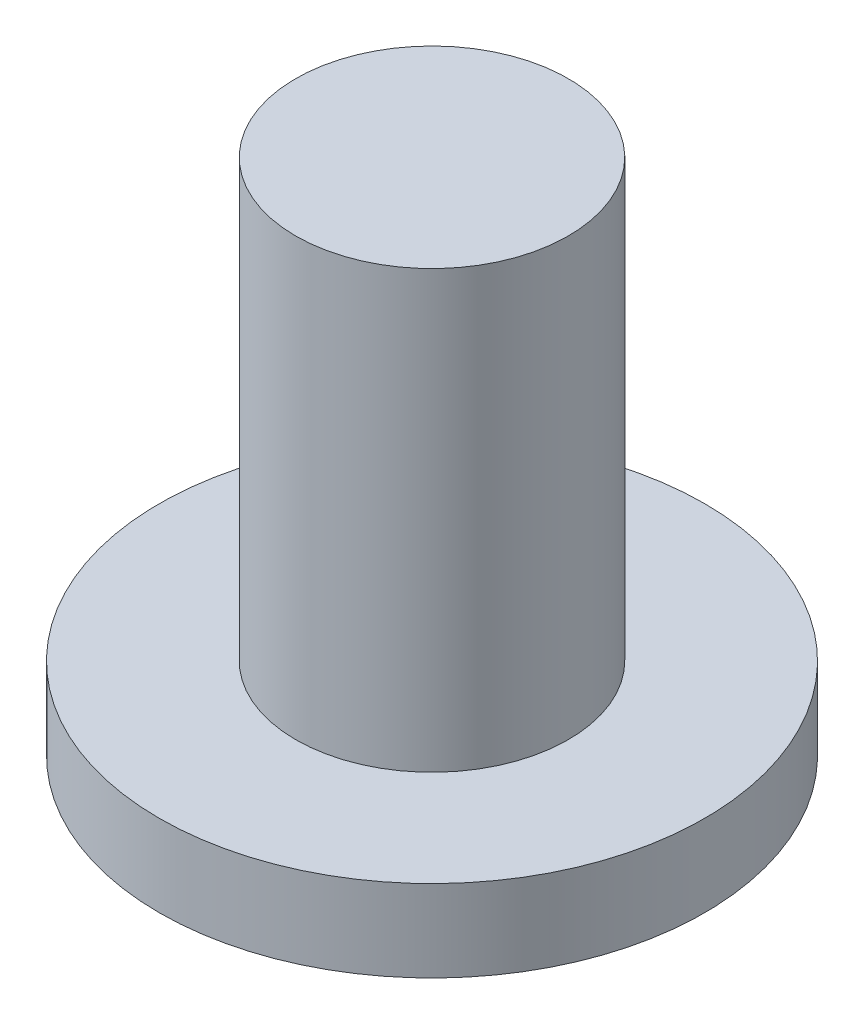
SolidWorks part; units mm, degrees
ref_plane "前视基准面" through (0, 0, 0) normal (0, 0, 1) x (1, 0, 0)
ref_plane "上视基准面" through (0, 0, 0) normal (0, 1, 0) x (1, 0, 0)
ref_plane "右视基准面" through (0, 0, 0) normal (1, 0, 0) x (0, 0, -1)
sketch "草图1" plane through (0, 0, 0) normal (0, 1, 0) x (1, 0, 0)
  circle A0 centre (0, 0) radius 10
  dimension "D1" = 20
extrude "凸台-拉伸1" add sketch "草图1" along normal blind 3
sketch "草图3" plane through (0, 3, 0) normal (0, 1, 0) x (1, 0, 0)
  circle A0 centre (0, 0) radius 5
  dimension "D1" = 10
extrude "凸台-拉伸2" add sketch "草图3" along normal blind 16
